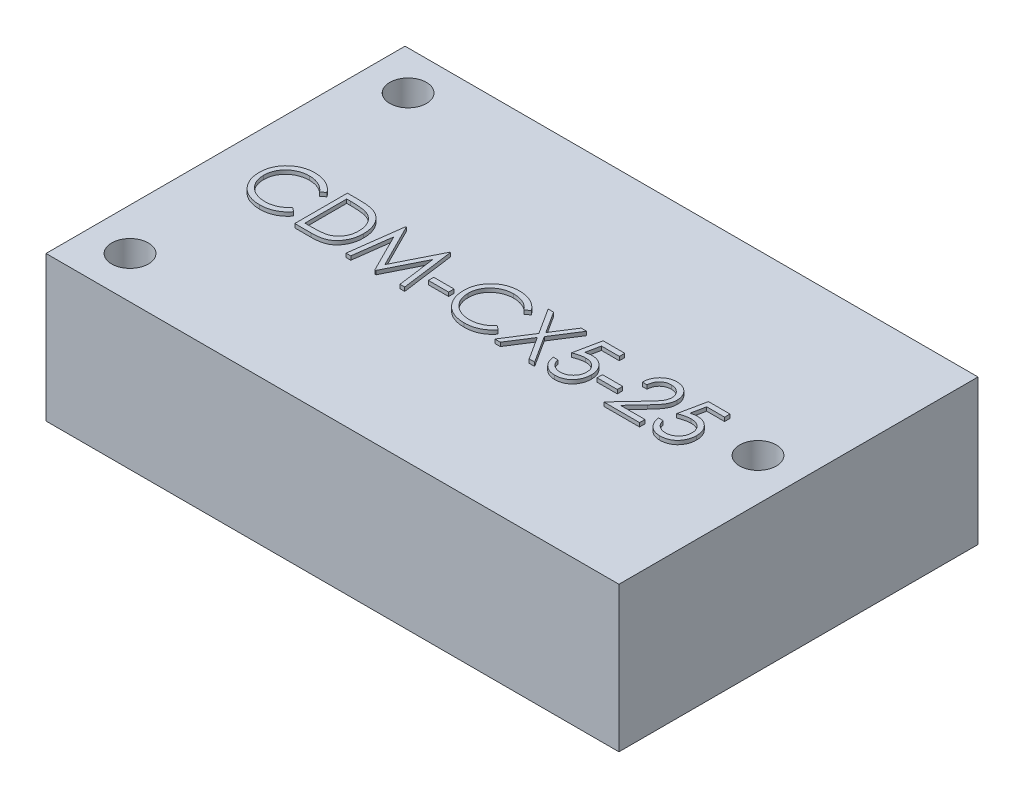
SolidWorks part; units mm, degrees
ref_plane "Front Plane" through (0, 0, 0) normal (0, 0, 1) x (1, 0, 0)
ref_plane "Top Plane" through (0, 0, 0) normal (0, 1, 0) x (1, 0, 0)
ref_plane "Right Plane" through (0, 0, 0) normal (1, 0, 0) x (0, 0, -1)
sketch "Sketch1" plane through (0, 0, 0) normal (0, 1, 0) x (1, 0, 0)
  line L1 (-19.05, 11.938) -> (19.05, 11.938)
  line L2 (-19.05, 11.938) -> (-19.05, -11.938)
  line L3 (-19.05, -11.938) -> (19.05, -11.938)
  line L4 (19.05, 11.938) -> (19.05, -11.938)
  line L5 (-19.05, 11.938) -> (19.05, -11.938) construction
  line L6 (-19.05, -11.938) -> (19.05, 11.938) construction
  circle A0 centre (-16.256, 9.3472) radius 1.2192
  circle A1 centre (-16.256, -9.144) radius 1.2192
  circle A2 centre (16.256, 0.1016) radius 1.2192
  point P0 (0, 0)
  point P14 (-17.4531, -10.9373)
  dimension "D3" = 2.4384
  dimension "D4" = 2.4384
  dimension "D5" = 2.4384
  dimension "D1" = 38.1
  dimension "D2" = 23.876
  dimension "D6" = 18.4912
  dimension "D7" = 2.794
  dimension "D8" = 2.794
  dimension "D9" = 32.512
  dimension "D10" = 12.0396
  dimension "D11" = 2.794
extrude "Boss-Extrude1" add sketch "Sketch1" against normal blind 9.652
sketch "Sketch2" plane through (0, 0, 0) normal (0, 1, 0) x (1, 0, 0)
  text T0 "CDM-CX5-25"
extrude "Boss-Extrude2" add sketch "Sketch2" along normal blind 0.254
